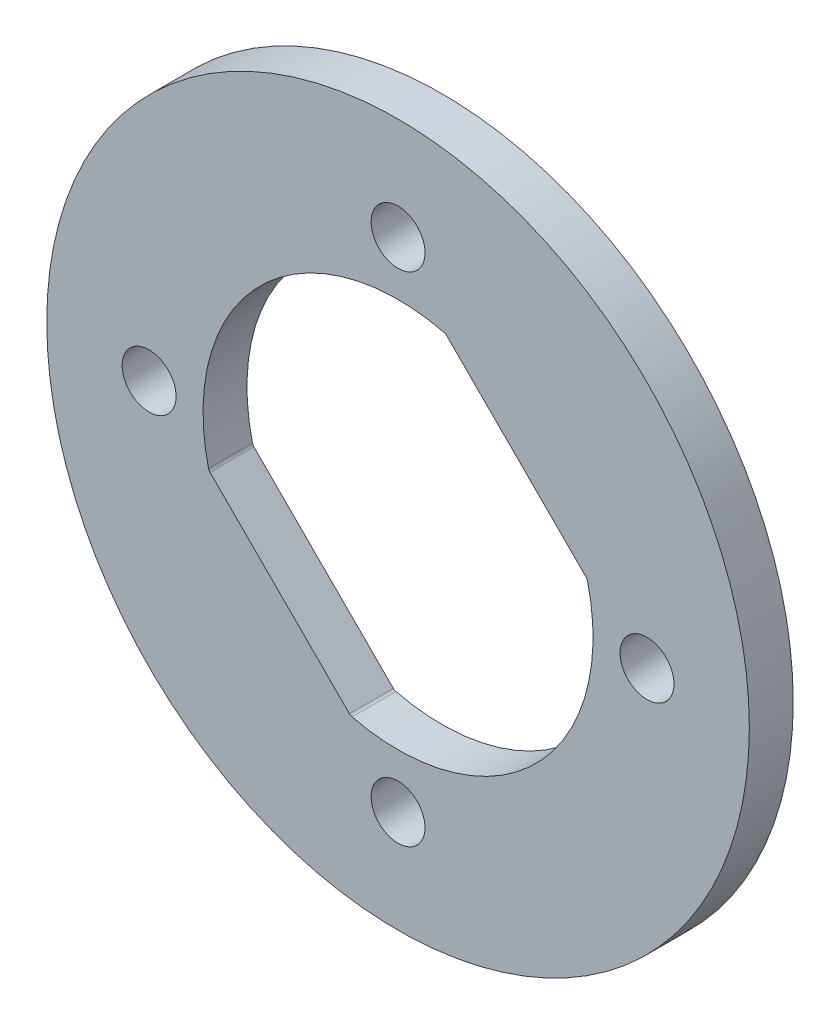
SolidWorks part; units mm, degrees
ref_plane "Front Plane" through (0, 0, 0) normal (0, 0, 1) x (1, 0, 0)
ref_plane "Top Plane" through (0, 0, 0) normal (0, 1, 0) x (1, 0, 0)
ref_plane "Right Plane" through (0, 0, 0) normal (1, 0, 0) x (0, 0, -1)
sketch "Sketch3" plane through (0, 0, 0) normal (0, 0, 1) x (1, 0, 0)
  line L10 (-6.7979, -1.7581) -> (-1.7581, -6.7979)
  line L11 (6.7979, 1.7581) -> (1.7581, 6.7979)
  line L12 (-6.2696, 8.8858) -> (-5.0558, 7.6721)
  line L13 (-7.6721, 5.0558) -> (-8.8858, 6.2696)
  line L14 (-8.8858, -6.2696) -> (-7.6721, -5.0558)
  line L15 (-5.0558, -7.6721) -> (-6.2696, -8.8858)
  line L16 (6.2696, -8.8858) -> (5.0558, -7.6721)
  line L17 (7.6721, -5.0558) -> (8.8858, -6.2696)
  line L18 (8.8858, 6.2696) -> (7.6721, 5.0558)
  line L19 (5.0558, 7.6721) -> (6.2696, 8.8858)
  arc A19 (-7.6721, 5.0558) -> (-5.0558, 7.6721) centre (-6.364, 6.364) ccw
  arc A20 (-8.8858, 6.2696) -> (-8.8858, -6.2696) centre (0, 0) ccw
  arc A21 (-5.0558, -7.6721) -> (-7.6721, -5.0558) centre (-6.364, -6.364) ccw
  arc A22 (-6.2696, -8.8858) -> (6.2696, -8.8858) centre (0, 0) ccw
  arc A23 (7.6721, -5.0558) -> (5.0558, -7.6721) centre (6.364, -6.364) ccw
  arc A24 (8.8858, -6.2696) -> (8.8858, 6.2696) centre (0, 0) ccw
  arc A25 (5.0558, 7.6721) -> (7.6721, 5.0558) centre (6.364, 6.364) ccw
  arc A26 (6.2696, 8.8858) -> (-6.2696, 8.8858) centre (0, 0) ccw
  circle A27 centre (-9, 0) radius 0.975
  circle A28 centre (0, -9) radius 0.975
  arc A29 (1.7581, 6.7979) -> (1.6639, 6.8508) centre (1.6167, 6.6565) ccw
  arc A30 (-6.8508, -1.6639) -> (-6.7979, -1.7581) centre (-6.6565, -1.6167) ccw
  arc A31 (1.6639, 6.8508) -> (-6.8508, -1.6639) centre (0, 0) ccw
  arc A32 (-1.7581, -6.7979) -> (-1.6639, -6.8508) centre (-1.6167, -6.6565) ccw
  arc A33 (-1.6639, -6.8508) -> (6.8508, 1.6639) centre (0, 0) ccw
  arc A34 (6.8508, 1.6639) -> (6.7979, 1.7581) centre (6.6565, 1.6167) ccw
  circle A35 centre (9, 0) radius 0.975
  circle A36 centre (0, 9) radius 0.975
  circle A37 centre (0, 0) radius 12.7
  dimension "D1" = 1.95
  dimension "D2" = 25.4
extrude "Boss-Extrude2" add sketch "Sketch3" along normal blind 1.5875 contours A37 A26 L19 A25 L18 A24 L17 A23 L16 A22 L15 A21 L14 A20 L13 A19 L12 | L19 A26 L12 A19 L13 A20 L14 A21 L15 A22 L16 A23 L17 A24 L18 A25 A36 A35 A34 A33 A32 L10 A30 A31 A29 L11 A28 A27
